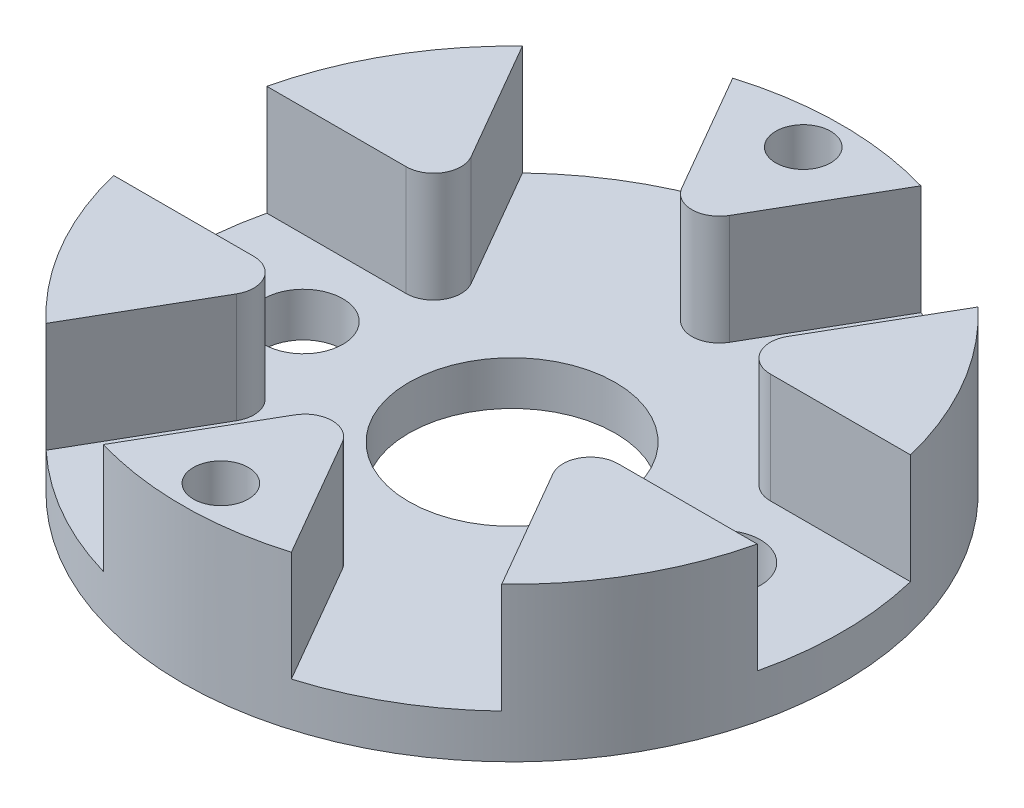
SolidWorks part; units mm, degrees
ref_plane "Front" through (0, 0, 0) normal (0, 0, 1) x (1, 0, 0)
ref_plane "Top" through (0, 0, 0) normal (0, 1, 0) x (1, 0, 0)
ref_plane "Right" through (0, 0, 0) normal (1, 0, 0) x (0, 0, -1)
sketch "Sketch1" plane through (0, 0, 0) normal (0, 1, 0) x (1, 0, 0)
  circle A0 centre (0, 0) radius 15
  circle A1 centre (0, 0) radius 4.7
  dimension "D1" = 30
  dimension "D2" = 9.4
extrude "Base" add sketch "Sketch1" along normal blind 2
sketch "Sketch2" plane through (0, 2, 0) normal (0, 1, 0) x (1, 0, 0)
  line L1 (6.0285, 3.5577) -> (14.5714, 3.56)
  line L2 (-0.0668, 6.9997) -> (4.2027, 14.3992)
  line L4 (-4.3213, 14.3641) -> (-0.0668, 6.9997)
  line L6 (10.279, 10.9244) -> (6.0285, 3.5577)
  line L7 (6.0953, -3.442) -> (10.3688, -10.8392)
  line L9 (14.6003, -3.4397) -> (6.0953, -3.442)
  line L10 (0.0668, -6.9997) -> (-4.2027, -14.3992)
  line L12 (4.3213, -14.3641) -> (0.0668, -6.9997)
  line L13 (-6.0285, -3.5577) -> (-14.5714, -3.56)
  line L15 (-10.279, -10.9244) -> (-6.0285, -3.5577)
  line L16 (-6.0953, 3.442) -> (-10.3688, 10.8392)
  line L18 (-14.6003, 3.4397) -> (-6.0953, 3.442)
  line L19 (3.2375, 13.7553) -> (-3.6907, 13.7534) [skipped]
  circle A0 centre (-0.068, 11.5028) radius 2.2516 construction
  circle A1 centre (9.9277, 5.8103) radius 2.2516 construction
  circle A2 centre (9.9958, -5.6925) radius 2.2516 construction
  circle A3 centre (0.068, -11.5028) radius 2.2516 construction
  circle A4 centre (-9.9277, -5.8103) radius 2.2516 construction
  circle A5 centre (-9.9958, 5.6925) radius 2.2516 construction
  arc A6 (-4.3213, 14.3641) -> (4.2027, 14.3992) centre (0, 0) cw
  arc A7 (10.279, 10.9244) -> (14.5714, 3.56) centre (0, 0) cw
  arc A8 (14.6003, -3.4397) -> (10.3688, -10.8392) centre (0, 0) cw
  arc A9 (4.3213, -14.3641) -> (-4.2027, -14.3992) centre (0, 0) cw
  arc A10 (-10.279, -10.9244) -> (-14.5714, -3.56) centre (0, 0) cw
  arc A11 (-14.6003, 3.4397) -> (-10.3688, 10.8392) centre (0, 0) cw
  circle A12 centre (0, 0) radius 15 construction
  point P34 (0, 0)
  dimension "D1" = 6
  dimension "D2" = 14
extrude "Triangles" add sketch "Sketch2" along normal blind 5
fillet "Fillet1" radius 1.25 6 edges at (6.0953, 4.5, 3.442) (0.0668, 4.5, 6.9997) (-6.0285, 4.5, 3.5577) (-6.0953, 4.5, -3.442) (6.0285, 4.5, -3.5577) (-0.0668, 4.5, -6.9997)
sketch "Sketch3" plane through (0, 2, 0) normal (0, 1, 0) x (1, 0, 0)
  line L0 (0, 0) -> (-9.5, 0) construction
  line L1 (0, 0) -> (9.5, 0) construction
  circle A0 centre (-9.5, 0) radius 1.8
  circle A1 centre (9.5, 0) radius 1.8
  dimension "D2" = 3.6
  dimension "D1" = 19
extrude "Wheel Holes" cut sketch "Sketch3" against normal up to next
sketch "Sketch4" plane through (0, 7, 0) normal (0, 1, 0) x (1, 0, 0)
  line L0 (0, 0) -> (0, 13.25) construction
  line L1 (0, 0) -> (0, -13.25) construction
  circle A0 centre (0, 13.25) radius 1.25
  circle A1 centre (0, -13.25) radius 1.25
  dimension "D2" = 2.5
  dimension "D1" = 26.5
extrude "Horn Holes" cut sketch "Sketch4" against normal through all
